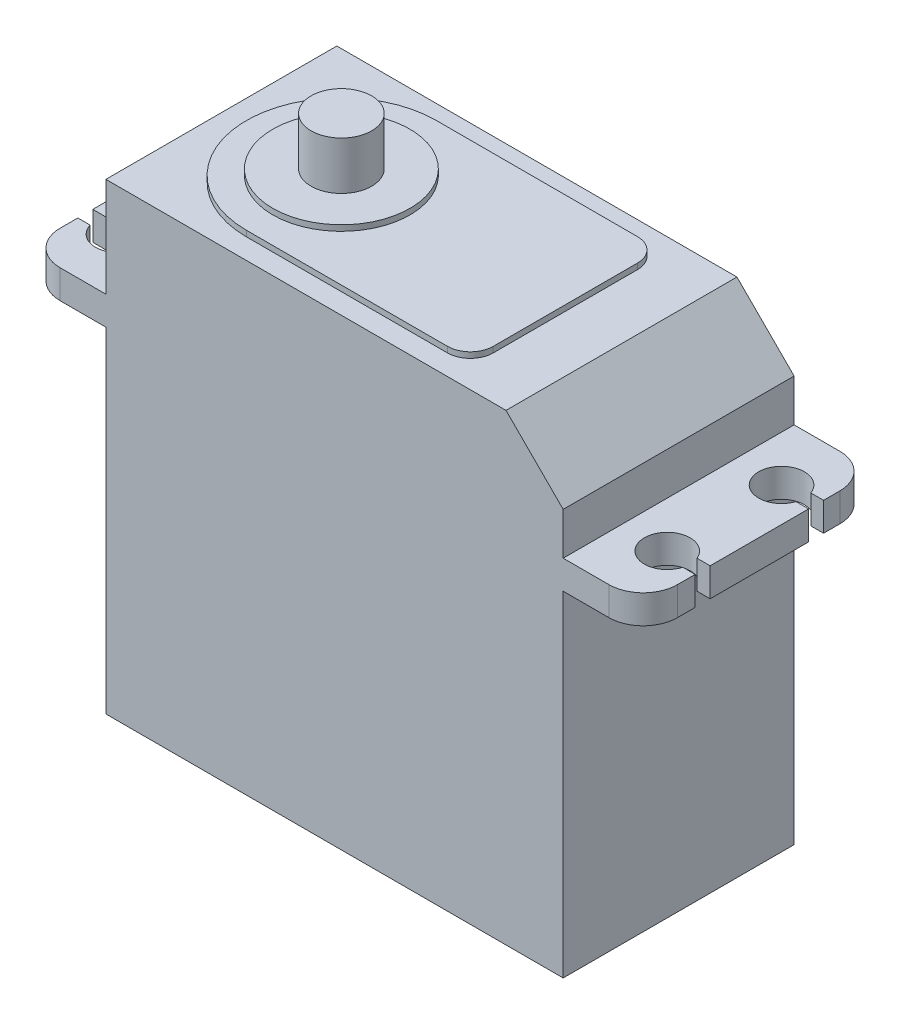
SolidWorks part; units mm, degrees
ref_plane "Front Plane" through (0, 0, 0) normal (0, 0, 1) x (1, 0, 0)
ref_plane "Top Plane" through (0, 0, 0) normal (0, 1, 0) x (1, 0, 0)
ref_plane "Right Plane" through (0, 0, 0) normal (1, 0, 0) x (0, 0, -1)
sketch "Sketch1" plane through (0, 0, 0) normal (0, 0, 1) x (1, 0, 0)
  line L1 (-20, -14.65) -> (20, -14.65)
  line L2 (-20, -14.65) -> (-20, 14.65)
  line L3 (-20, 14.65) -> (20, 14.65)
  line L4 (20, -14.65) -> (20, 14.65)
  line L5 (-20, -14.65) -> (20, 14.65) construction
  line L6 (-20, 14.65) -> (20, -14.65) construction
  line L7 (27, 14.65) -> (-27, 14.65)
  line L8 (27, 14.65) -> (27, 17.15)
  line L9 (27, 17.15) -> (-27, 17.15)
  line L10 (-27, 14.65) -> (-27, 17.15)
  line L11 (27, 14.65) -> (-27, 17.15) construction
  line L12 (27, 17.15) -> (-27, 14.65) construction
  line L13 (-20, 17.15) -> (20, 17.15)
  line L14 (-20, 17.15) -> (-20, 25.85)
  line L15 (-20, 25.85) -> (20, 25.85)
  line L16 (20, 17.15) -> (20, 25.85)
  line L17 (-20, 17.15) -> (20, 25.85) construction
  line L18 (-20, 25.85) -> (20, 17.15) construction
  point P0 (0, 0)
  point P10 (0, 15.9)
  point P11 (0, 0)
  point P16 (0, 21.5)
  point P17 (0, 0)
  dimension "D1" = 29.3
  dimension "D2" = 40
  dimension "D3" = 2.5
  dimension "D4" = 54
  dimension "D5" = 8.7
  dimension "D6" = 40
extrude "Boss-Extrude1" add sketch "Sketch1" along normal blind 20.2 contours L1 L4 L3 L2 | L10 L7 L3 L8 L9 | L9 L16 L15 L14
sketch "Sketch2" plane through (0, 25.85, 0) normal (0, 1, 0) x (1, 0, 0)
  line L0 (-20, -20.2) -> (-20, 0) construction
  line L1 (-20, -20.2) -> (-20, 0) construction
  circle A0 centre (-9.5, -10.1) radius 2.65
  point P6 (-20, -10.1)
  dimension "D1" = 10.5
  dimension "D2" = 5.3
extrude "Boss-Extrude2" add sketch "Sketch2" along normal blind 5.2
sketch "Sketch3" plane through (0, 17.15, 0) normal (0, 1, 0) x (1, 0, 0)
  line L0 (24, -5.1) -> (24, -15.1) construction
  line L1 (-20, -20.2) -> (-20, 0) construction
  line L2 (0, 7.0857) -> (0, -23.7217) construction
  line L5 (-25.5406, -14.3469) -> (-27.4468, -14.3469)
  line L6 (25.5406, -5.7312) -> (27.4468, -5.7312)
  line L7 (25.5406, -5.7312) -> (25.5406, -4.4251)
  line L8 (25.5406, -4.4251) -> (27.4468, -4.4251)
  line L9 (27.4468, -5.7312) -> (27.4468, -4.4251)
  line L10 (25.5406, -5.7312) -> (27.4468, -4.4251) construction
  line L11 (25.5406, -4.4251) -> (27.4468, -5.7312) construction
  line L12 (25.5406, -15.6531) -> (27.4468, -15.6531)
  line L13 (25.5406, -15.6531) -> (25.5406, -14.3469)
  line L14 (25.5406, -14.3469) -> (27.4468, -14.3469)
  line L15 (27.4468, -15.6531) -> (27.4468, -14.3469)
  line L16 (25.5406, -15.6531) -> (27.4468, -14.3469) construction
  line L17 (25.5406, -14.3469) -> (27.4468, -15.6531) construction
  line L18 (-27.4468, -15.6531) -> (-27.4468, -14.3469)
  line L19 (-25.5406, -15.6531) -> (-27.4468, -15.6531)
  line L20 (-25.5406, -15.6531) -> (-25.5406, -14.3469)
  line L21 (-25.5406, -4.4251) -> (-27.4468, -4.4251)
  line L22 (-27.4468, -5.7312) -> (-27.4468, -4.4251)
  line L23 (-25.5406, -5.7312) -> (-27.4468, -5.7312)
  line L24 (-25.5406, -5.7312) -> (-25.5406, -4.4251)
  circle A0 centre (24, -5.1) radius 2
  circle A1 centre (24, -15.1) radius 2
  circle A2 centre (-24, -15.1) radius 2
  circle A3 centre (-24, -5.1) radius 2
  point P7 (-20, -10.1)
  point P8 (24, -10.1)
  point P15 (26.4937, -5.0781)
  point P20 (26.4937, -15)
  line M5 (27, -20.2) -> (27, 0)
  dimension "D1" = 4
  dimension "D2" = 4
  dimension "D3" = 24
  dimension "D4" = 10
extrude "Cut-Extrude1" cut sketch "Sketch3" against normal blind 5.2 contours A3 L21 L24 L23 | A3 L23 L24 L21 | L23 A3 L21 L22 | A2 L5 L20 L19 | A2 L19 L20 L5 | L19 A2 L5 L18 | L6 L9 L8 M5 | A0 L6 L8 M5 | L6 A0 L8 L7 | L8 A0 L6 L7 | L12 L15 L14 M5 | A1 L12 L14 M5 | L12 A1 L14 L13 | L14 A1 L12 L13
fillet "Fillet1" radius 3 4 edges at (27, 15.9, 20.2) (27, 15.9, 0) (-27, 15.9, 0) (-27, 15.9, 20.2)
chamfer "Chamfer1" distance 5 angle 45 1 edges at (20, 25.85, 10.1)
sketch "Sketch4" plane through (0, 25.85, 0) normal (0, 1, 0) x (1, 0, 0)
  circle A0 centre (-9.5, -10.1) radius 6
  dimension "D1" = 12
extrude "Boss-Extrude3" add sketch "Sketch4" along normal blind 1
sketch "Sketch5" plane through (0, 25.85, 0) normal (0, 1, 0) x (1, 0, 0)
  line L0 (-9.5, -1.7899) -> (8.0921, -1.7899)
  line L1 (10.0921, -3.7899) -> (10.0921, -16.4101)
  line L2 (8.0921, -18.4101) -> (-9.5, -18.4101)
  arc A0 (-9.5, -1.7899) -> (-9.5, -18.4101) centre (-9.5, -10.1) ccw
  arc A1 (10.0921, -16.4101) -> (8.0921, -18.4101) centre (8.0921, -16.4101) cw
  arc A2 (10.0921, -3.7899) -> (8.0921, -1.7899) centre (8.0921, -3.7899) ccw
  dimension "D1" = 180
  dimension "D2" = 2
extrude "Boss-Extrude4" add sketch "Sketch5" along normal blind 0.5
